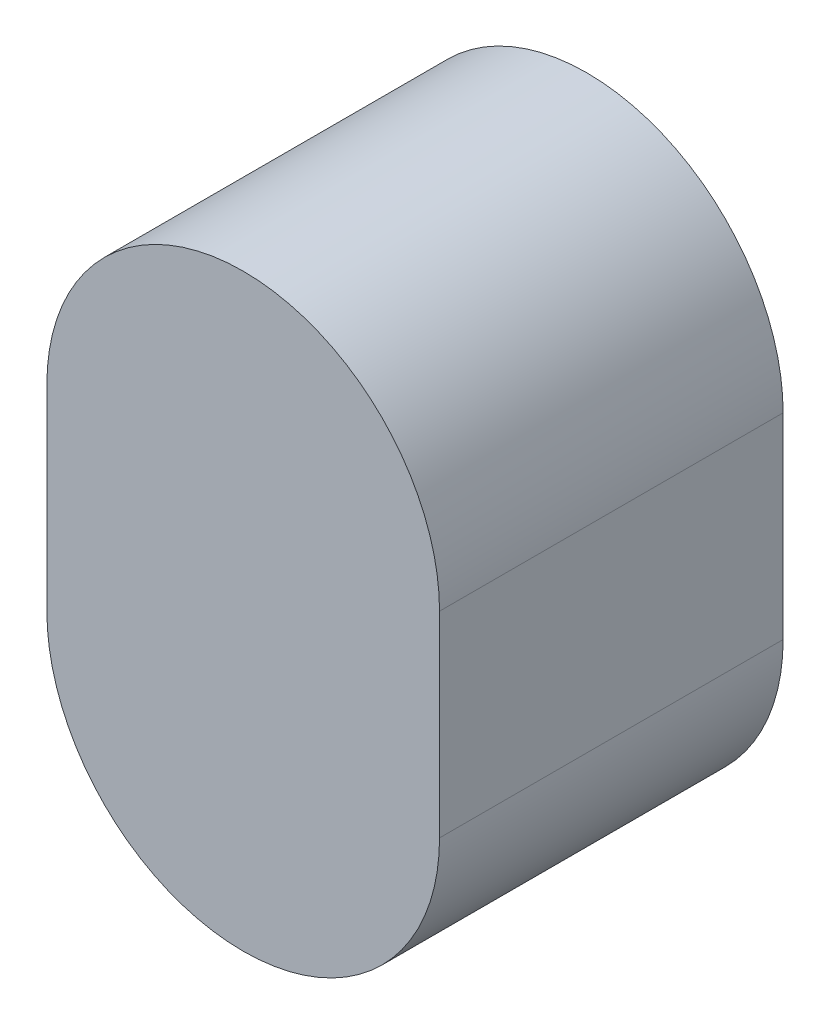
SolidWorks part; units mm, degrees
ref_plane "Front Plane" through (0, 0, 0) normal (0, 0, 1) x (1, 0, 0)
ref_plane "Top Plane" through (0, 0, 0) normal (0, 1, 0) x (1, 0, 0)
ref_plane "Right Plane" through (0, 0, 0) normal (1, 0, 0) x (0, 0, -1)
sketch "Sketch1" plane through (0, 0, 0) normal (0, 0, 1) x (1, 0, 0)
  line L0 (0, 0) -> (-4, 0)
  line L1 (0, 0) -> (4, 0)
  line L2 (0, 0) -> (0, -4)
  line L3 (0, 0) -> (0, -4) construction
  line L4 (4, 0) -> (4, -4)
  line L5 (-4, 0) -> (-4, -4)
  arc A0 (4, 0) -> (-4, 0) centre (0, 0) ccw
  arc A1 (-4, -4) -> (4, -4) centre (0, -4) ccw
  point P3 (0, -2)
extrude "Boss-Extrude1" add sketch "Sketch1" along normal blind 7 contours A0 L5 A1 L4
